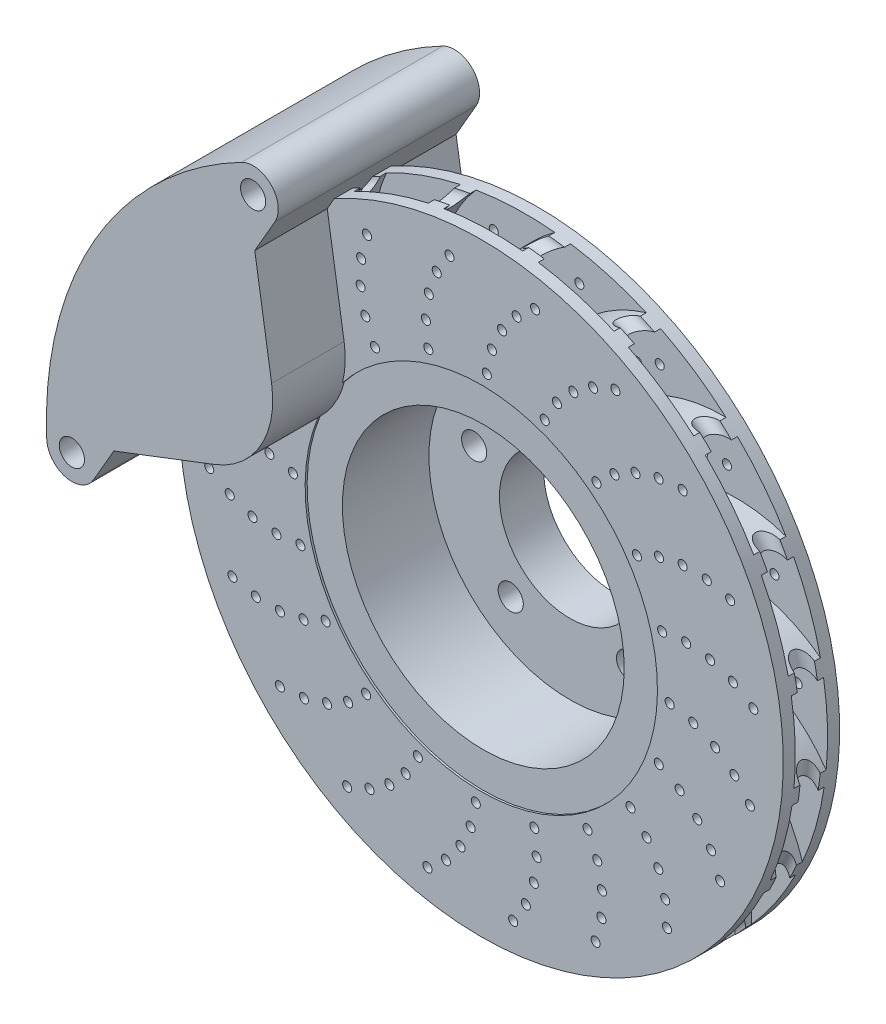
SolidWorks part; units mm, degrees
ref_plane "Front Plane" through (0, 0, 0) normal (0, 0, 1) x (1, 0, 0)
ref_plane "Top Plane" through (0, 0, 0) normal (0, 1, 0) x (1, 0, 0)
ref_plane "Right Plane" through (0, 0, 0) normal (1, 0, 0) x (0, 0, -1)
sketch "Sketch1" plane through (0, 0, 0) normal (1, 0, 0) x (0, 0, -1)
  line L0 (-35.4665, 0) -> (124.4653, 0) construction
  line L1 (-7.0104, 87.5) -> (-7.0104, 70)
  line L2 (-8.0104, 150) -> (-2.0104, 150)
  line L3 (-8.0104, 150) -> (-8.0104, 87.5)
  line L4 (-8.0104, 87.5) -> (-7.0104, 87.5)
  line L5 (-2.0104, 150) -> (-2.0104, 87.5)
  line L6 (19.9896, 150) -> (13.9896, 150)
  line L7 (19.9896, 150) -> (19.9896, 87.5)
  line L8 (19.9896, 87.5) -> (13.9896, 87.5)
  line L13 (13.9896, 150) -> (13.9896, 87.5)
  line L14 (-7.0104, 70) -> (35.9896, 70)
  line L15 (35.9896, 70) -> (35.9896, 35)
  line L16 (35.9896, 35) -> (57.9896, 35)
  line L17 (57.9896, 35) -> (57.9896, 77.5)
  line L18 (57.9896, 77.5) -> (-3.0104, 77.5)
  line L19 (-3.0104, 77.5) -> (-3.0104, 87.5)
  line L20 (-3.0104, 87.5) -> (-2.0104, 87.5)
  dimension "D1" = 150
  dimension "D2" = 70
  dimension "D3" = 35
  dimension "D4" = 42.5
  dimension "D5" = 10
  dimension "D6" = 22
  dimension "D7" = 1
  dimension "D8" = 1
  dimension "D9" = 6
  dimension "D10" = 6
  dimension "D11" = 150
  dimension "D12" = 22
  dimension "D13" = 65
  dimension "D14" = 0
revolve "Revolve1" add sketch "Sketch1" angle 360 about L0
sketch "Sketch2" plane through (0, 0, -57.9896) normal (0, 0, -1) x (-1, 0, 0)
  line L0 (0, 0) -> (0, 50) construction
  circle A0 centre (0, 50) radius 6.25
  circle A1 centre (47.5528, 15.4508) radius 6.25
  circle A2 centre (29.3893, -40.4508) radius 6.25
  circle A3 centre (-29.3893, -40.4508) radius 6.25
  circle A4 centre (-47.5528, 15.4508) radius 6.25
  dimension "D2" = 12.5
  dimension "D1" = 50
  dimension "D3" = 5
extrude "Cut-Extrude2" cut sketch "Sketch2" against normal through all
sketch "Sketch3" plane through (0, 0, 0) normal (0, 0, 1) x (1, 0, 0)
  arc A0 (47.5528, 15.4508) -> (122.5528, 86.4916) centre (98.0472, 37.2527) cw
  circle A1 centre (0, 0) radius 150 construction
  circle A2 centre (57.2085, 74.093) radius 2.25
  circle A3 centre (66.1503, 82.0588) radius 2.25
  circle A4 centre (76.6042, 87.9005) radius 2.25
  circle A5 centre (88.0746, 91.3411) radius 2.25
  circle A6 centre (100.0179, 92.2174) radius 2.25
  dimension "D2" = 55
  dimension "D3" = 4.5
  dimension "D1" = 75
  dimension "D4" = 5
extrude "Cut-Extrude7" cut sketch "Sketch3" against normal mid plane 100 contours A6 | A5 | A4 | A3 | A2
sketch "Sketch4" plane through (0, 0, 8.0104) normal (0, 0, 1) x (1, 0, 0)
  circle A2 centre (0, 0) radius 140
  circle A3 centre (0, 0) radius 140
  dimension "D1" = 10
sketch "Sketch5" plane through (0, 0, 8.0104) normal (0, 0, 1) x (1, 0, 0)
  circle A2 centre (88.0746, 91.3411) radius 2.25 construction
  circle A4 centre (76.6042, 87.9005) radius 2.25 construction
  circle A6 centre (57.2085, 74.093) radius 2.25 construction
  circle A8 centre (57.2085, 74.093) radius 2.25 construction
  circle A10 centre (100.0179, 92.2174) radius 2.25 construction
  arc A12 (105.2439, 106.8818) -> (40.733, 77.4408) centre (98.0472, 37.2527) ccw
  arc A13 (99.5115, 112.2384) -> (36.1908, 79.6648) centre (98.0472, 37.2527) ccw
  circle A14 centre (0, 0) radius 87.5 construction
  circle A15 centre (0, 0) radius 150 construction
  arc A16 (40.733, 77.4408) -> (36.1908, 79.6648) centre (0, 0) ccw
  arc A17 (105.2439, 106.8818) -> (99.5115, 112.2384) centre (0, 0) ccw
  arc A18 (131.464, 104.3967) -> (29.1912, 7.5229) centre (98.0472, 37.2527) ccw construction
  arc A19 (129.2362, 99.9204) -> (33.7816, 9.5049) centre (98.0472, 37.2527) ccw construction
  dimension "D7" = 5
extrude "Boss-Extrude3" add sketch "Sketch5" against normal up to surface (22 mm away) up to face at (97.7679, 92.2174, -13.9896)
pattern_circular "CirPattern2" count 20 over 360 about axis through (0, 0, 0) along (0, 0, 1) of "Cut-Extrude7", "Boss-Extrude3"
sketch "Sketch7" plane through (0, 0, 0) normal (1, 0, 0) x (0, 0, -1)
  line L0 (-8.0104, -150) -> (19.9896, -150) construction
  line L1 (57.9896, 0) -> (112.2848, 0) construction
  line L2 (57.9896, -77.5) -> (57.9896, 77.5) construction
  circle A0 centre (5.9896, -150) radius 5
  circle A1 centre (5.9896, -87.5) radius 5
  dimension "D1" = 10
  dimension "D2" = 62.5
revolve "Cut-Revolve1" cut sketch "Sketch7" angle 360 about L1
ref_plane "Plane1" through (0, 0, -5.9896) normal (0, 0, -1) x (-1, 0, 0)
sketch "Sketch8" plane through (0, 0, -5.9896) normal (0, 0, -1) x (-1, 0, 0)
  line L0 (0, 0) -> (240.6057, 0) construction
  line L1 (0, 0) -> (155.8846, 90) construction
  line L2 (122.3405, 70.6333) -> (77.3405, 148.5756) construction
  line L3 (76.5151, 125.0051) -> (66.5151, 142.3256)
  line L4 (76.5151, 125.0051) -> (68.1359, 72.0305)
  line L5 (146.5151, 3.7615) -> (96.4482, 22.9922)
  line L6 (146.5151, 3.7615) -> (156.5151, -13.559)
  arc A0 (180, 0) -> (83.1121, 159.6633) centre (0, 0) ccw
  arc A1 (68.1359, 72.0305) -> (96.4482, 22.9922) centre (112.5833, 65) ccw
  arc A2 (83.1121, 159.6633) -> (66.5151, 142.3256) centre (77.3405, 148.5756) ccw
  arc A3 (90, 155.8846) -> (179.8286, -7.8544) centre (0, 0) cw
  arc A4 (179.8286, -7.8544) -> (156.5151, -13.559) centre (167.3405, -7.309) cw
  circle A5 centre (77.3405, 148.5756) radius 6.25
  circle A6 centre (167.3405, -7.309) radius 6.25
  dimension "D3" = 90
  dimension "D5" = 25
  dimension "D8" = 12.5
  dimension "D9" = 12.5
  dimension "D1" = 30
  dimension "D2" = 180
  dimension "D4" = 90
  dimension "D6" = 20
  dimension "D7" = 50
extrude "Boss-Extrude4" add sketch "Sketch8" along normal mid plane 100 contours A4 A3 A0 A2 L3 L4 A1 L5 L6 A6 A5
sketch "Sketch9" plane through (0, 0, -5.9896) normal (0, 0, -1) x (-1, 0, 0)
  circle A1 centre (0, 0) radius 165
  arc A2 (80.3518, 144.1131) -> (164.9815, -2.4699) centre (0, 0) ccw
  arc A3 (80.3518, 144.1131) -> (164.9815, -2.4699) centre (0, 0) ccw
  dimension "D1" = 15
